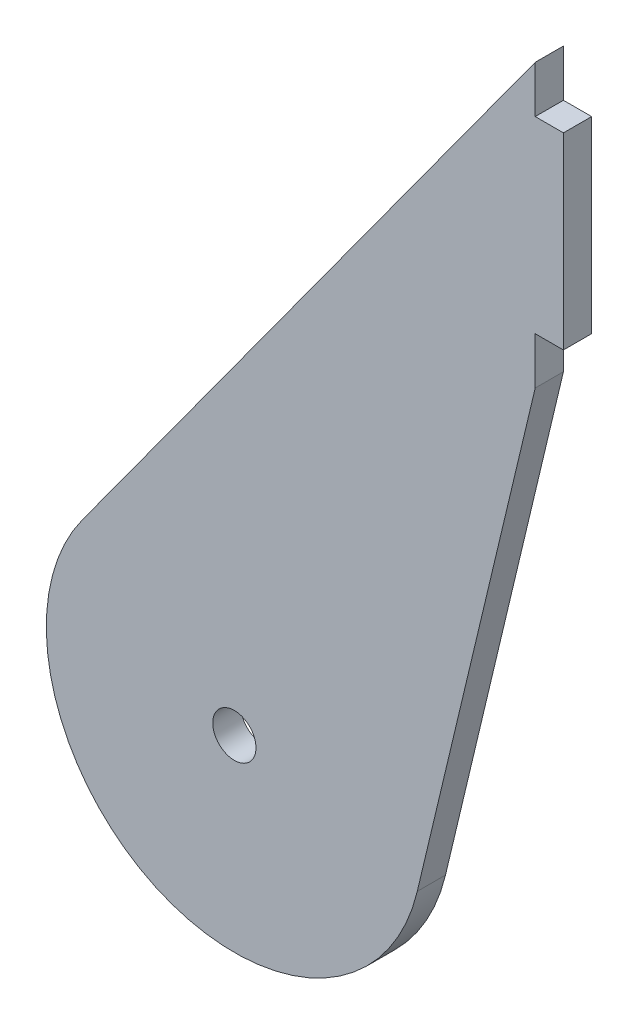
SolidWorks part; units mm, degrees
ref_plane "Front Plane" through (0, 0, 0) normal (0, 0, 1) x (1, 0, 0)
ref_plane "Top Plane" through (0, 0, 0) normal (0, 1, 0) x (1, 0, 0)
ref_plane "Right Plane" through (0, 0, 0) normal (1, 0, 0) x (0, 0, -1)
sketch "Sketch1" plane through (0, 0, 0) normal (0, 0, 1) x (1, 0, 0)
  line L0 (-16.1744, 11.7639) -> (32, 78)
  line L1 (32, 78) -> (32, 48)
  line L2 (32, 48) -> (19.4551, -4.6367)
  arc A0 (-16.1744, 11.7639) -> (19.4551, -4.6367) centre (0, 0) ccw
  dimension "D2" = 20
  dimension "D4" = 19.4551
  dimension "D5" = 32
  dimension "D6" = 16.1744
extrude "Boss-Extrude1" add sketch "Sketch1" against normal blind 3
sketch "Sketch2" plane through (0, 0, 0) normal (0, 0, 1) x (1, 0, 0)
  circle A0 centre (0, 0) radius 2.3
  dimension "D1" = 4.6
extrude "Cut-Extrude1" cut sketch "Sketch2" against normal blind 10
sketch "Sketch4" plane through (32, 0, 0) normal (1, 0, 0) x (0, 0, -1)
  line L0 (0, 48) -> (0, 78) construction
  line L1 (0, 73) -> (3, 73)
  line L2 (0, 73) -> (0, 53)
  line L3 (0, 53) -> (3, 53)
  line L4 (3, 73) -> (3, 53)
  line L5 (3, 48) -> (3, 78) construction
  line L6 (3, 48) -> (0, 48) construction
  dimension "D1" = 20
  dimension "D2" = 5
extrude "Boss-Extrude3" add sketch "Sketch4" along normal blind 3
